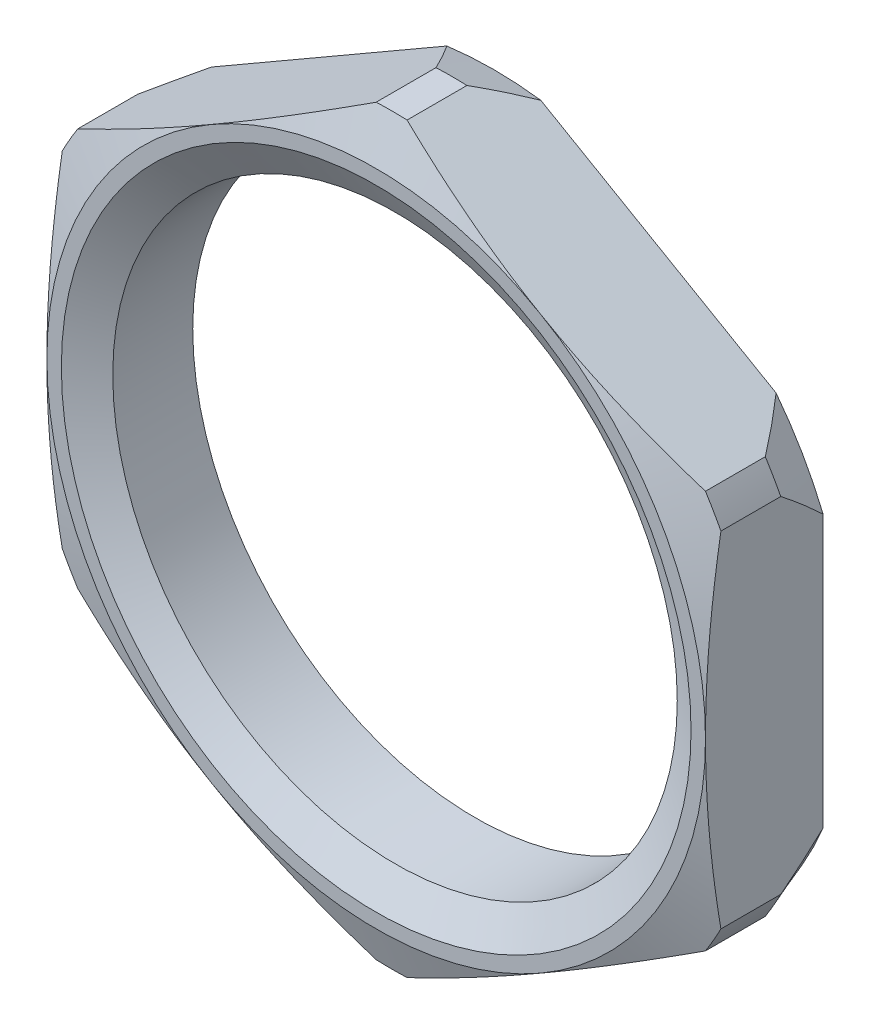
SolidWorks part; units mm, degrees
ref_plane "Front Plane" through (0, 0, 0) normal (0, 0, 1) x (1, 0, 0)
ref_plane "Top Plane" through (0, 0, 0) normal (0, 1, 0) x (1, 0, 0)
ref_plane "Right Plane" through (0, 0, 0) normal (1, 0, 0) x (0, 0, -1)
ref_plane "Plane1" through (0, 0, 6) normal (0, 0, -1) x (-1, 0, 0)
sketch "Sketch1" plane through (0, 0, 6) normal (0, 0, -1) x (-1, 0, 0)
  line L0 (-7, 3.662) -> (-7, -3.662)
  line L1 (-6.6714, -4.2312) -> (-0.3286, -7.8932)
  line L2 (0.3286, -7.8932) -> (6.6714, -4.2312)
  line L3 (7, -3.662) -> (7, 3.662)
  line L4 (6.6714, 4.2312) -> (0.3286, 7.8932)
  line L5 (-0.3286, 7.8932) -> (-6.6714, 4.2312)
  arc A0 (-7, -3.662) -> (-6.6714, -4.2312) centre (0, 0) ccw
  arc A1 (-0.3286, -7.8932) -> (0.3286, -7.8932) centre (0, 0) ccw
  arc A2 (6.6714, -4.2312) -> (7, -3.662) centre (0, 0) ccw
  arc A3 (7, 3.662) -> (6.6714, 4.2312) centre (0, 0) ccw
  arc A4 (0.3286, 7.8932) -> (-0.3286, 7.8932) centre (0, 0) ccw
  arc A5 (-6.6714, 4.2312) -> (-7, 3.662) centre (0, 0) ccw
extrude "Boss-Extrude1" add sketch "Sketch1" against normal blind 2.5
hole_wizard "Hole1" positions "Sketch3" profile "Sketch2" legacy
sketch "Sketch3" plane through (0, 0, 6) normal (0, 0, -1) x (-1, 0, 0)
  point P0 (0, 0)
sketch "Sketch2" plane through (0, 0, 6) normal (1, 0, 0) x (0, 1, 0)
  line L0 (0, 0) -> (0, 2.5)
  line L1 (0, 2.5) -> (6, 2.5)
  line L2 (6, 2.5) -> (6, 0)
  line L3 (6, 0) -> (0, 0)
  line L4 (0, 110) -> (0, -10) construction
  dimension "Diameter" = 12
  dimension "Depth" = 2.5
chamfer "Chamfer1" distance 0.9 angle 20 12 edges at (0, -7.9, 8.5) (-6.8416, 3.95, 8.5) (6.8416, 3.95, 8.5) (6.8416, 3.95, 6) (0, 7.9, 6) (6.8416, -3.95, 8.5) (-6.8416, 3.95, 6) (0, 7.9, 8.5) (-6.8416, -3.95, 6) (0, -7.9, 6) (6.8416, -3.95, 6) (-6.8416, -3.95, 8.5)
chamfer "Chamfer2" distance 0.6928 angle 30 1 edges at (-6, 0, 6)
chamfer "Chamfer3" distance 0.6928 angle 30 1 edges at (-6, 0, 8.5)
